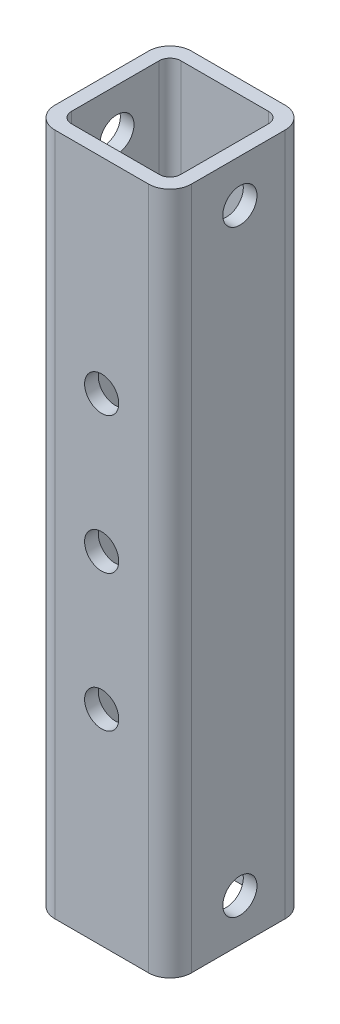
SolidWorks part; units mm, degrees
ref_plane "Front Plane" through (0, 0, 0) normal (0, 0, 1) x (1, 0, 0)
ref_plane "Top Plane" through (0, 0, 0) normal (0, 1, 0) x (1, 0, 0)
ref_plane "Right Plane" through (0, 0, 0) normal (1, 0, 0) x (0, 0, -1)
sketch "Sketch1" plane through (0, 0, 0) normal (0, 1, 0) x (1, 0, 0)
  line L1 (4, 0) -> (21.4, 0)
  line L2 (0, 4) -> (0, 21.4)
  line L3 (4, 25.4) -> (21.4, 25.4)
  line L4 (25.4, 4) -> (25.4, 21.4)
  line L6 (20.86, 2.54) -> (4.54, 2.54)
  line L7 (22.86, 4.54) -> (22.86, 20.86)
  line L8 (2.54, 4.54) -> (2.54, 20.86)
  line L9 (20.86, 22.86) -> (4.54, 22.86)
  line L10 (22.86, 2.54) -> (2.54, 22.86) construction
  line L11 (2.54, 2.54) -> (22.86, 22.86) construction
  arc A0 (2.54, 20.86) -> (4.54, 22.86) centre (4.54, 20.86) cw
  arc A1 (22.86, 20.86) -> (20.86, 22.86) centre (20.86, 20.86) ccw
  arc A2 (22.86, 4.54) -> (20.86, 2.54) centre (20.86, 4.54) cw
  arc A3 (4.54, 2.54) -> (2.54, 4.54) centre (4.54, 4.54) cw
  arc A4 (0, 21.4) -> (4, 25.4) centre (4, 21.4) cw
  arc A5 (21.4, 25.4) -> (25.4, 21.4) centre (21.4, 21.4) cw
  arc A6 (21.4, 0) -> (25.4, 4) centre (21.4, 4) ccw
  arc A7 (4, 0) -> (0, 4) centre (4, 4) cw
  point P9 (12.7, 12.7)
  point P31 (0, 0)
  dimension "D1" = 2
  dimension "D2" = 2
  dimension "D3" = 4
  dimension "D4" = 4
  dimension "D5" = 4
  dimension "D6" = 4
extrude "Boss-Extrude1" add sketch "Sketch1" along normal blind 127
sketch "Sketch2" plane through (0, 0, 0) normal (1, 0, 0) x (0, 0, -1)
  circle A0 centre (12.9921, 7.9375) radius 3.175
  circle A1 centre (12.9921, 119.0625) radius 3.175
extrude "Cut-Extrude1" cut sketch "Sketch2" along normal up to surface (25.4 mm away) up to face at (25.4, 63.5, -12.7)
sketch "Sketch3" plane through (0, 0, -25.4) normal (0, 0, -1) x (-1, 0, 0)
  circle A0 centre (-12.6995, 88.9) radius 3.175
  circle A1 centre (-12.6995, 63.5) radius 3.175
  circle A2 centre (-12.6995, 38.1) radius 3.175
extrude "Cut-Extrude2" cut sketch "Sketch3" against normal through all both and the other way through all
